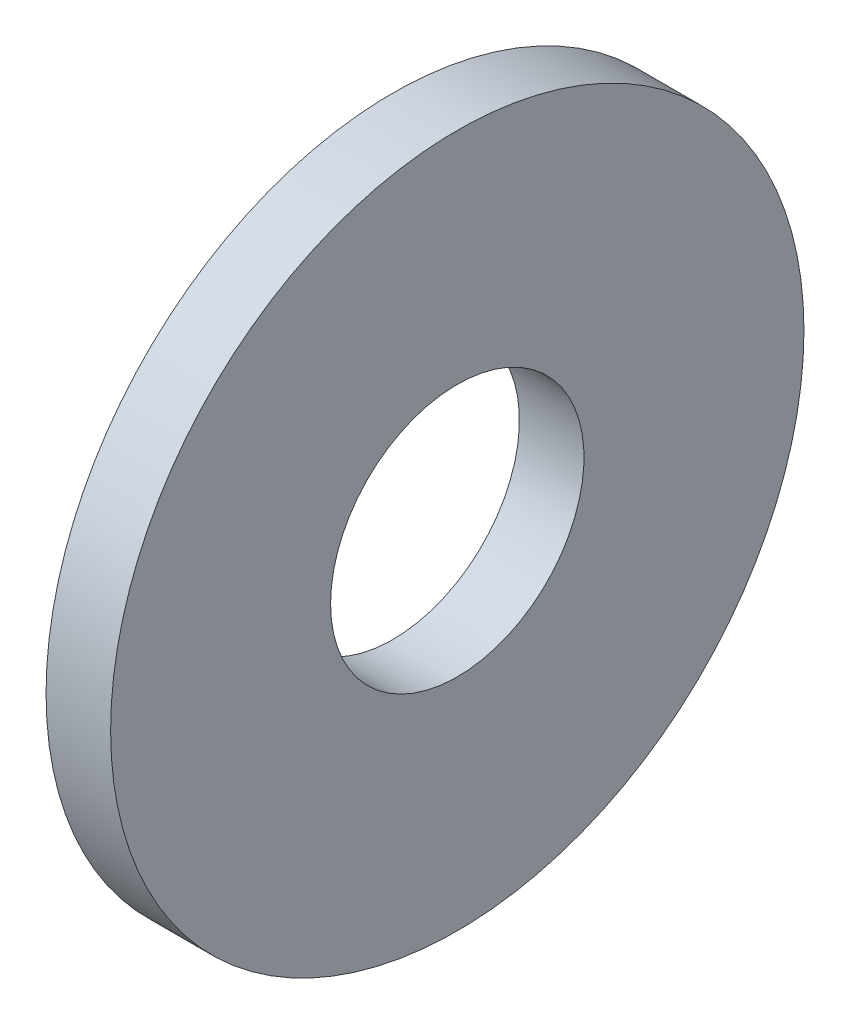
SolidWorks part; units mm, degrees
ref_plane "Plane1" through (0, 0, 0) normal (0, 0, 1) x (1, 0, 0)
ref_plane "Plane2" through (0, 0, 0) normal (0, 1, 0) x (1, 0, 0)
ref_plane "Plane3" through (0, 0, 0) normal (1, 0, 0) x (0, 0, -1)
sketch "Sketch1" plane through (0, 0, 0) normal (0, 0, 1) x (1, 0, 0)
  line L0 (-34.925, 0) -> (9.525, 0) construction
  line L1 (0, 3.435) -> (0, 9.4)
  line L2 (0, 9.4) -> (-1.75, 9.4)
  line L3 (-1.75, 9.4) -> (-1.75, 3.435)
  line L4 (-1.75, 3.435) -> (0, 3.435)
  dimension "Thickness" = 1.75
  dimension "Inside_dia" = 6.87
  dimension "Outside_dia" = 18.8
revolve "Base-Revolve" add sketch "Sketch1" angle 360 about L0
